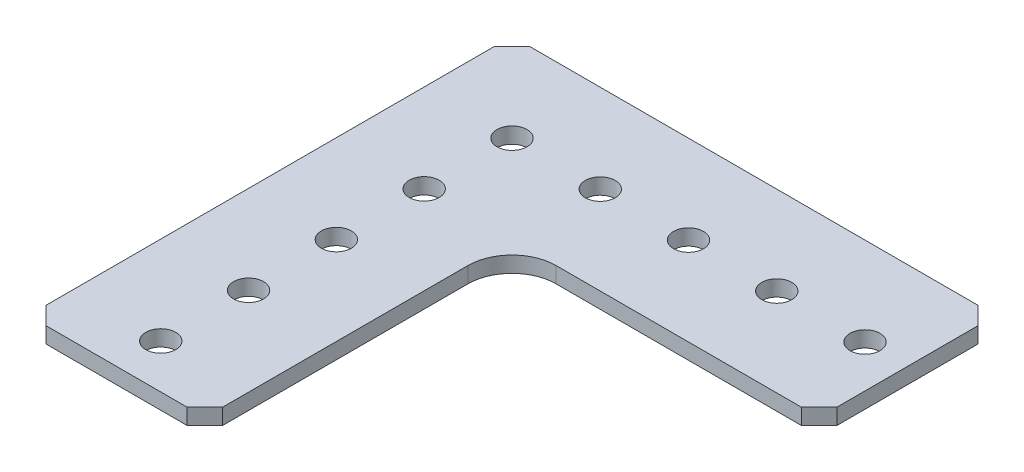
SolidWorks part; units mm, degrees
ref_plane "Front Plane" through (0, 0, 0) normal (0, 0, 1) x (1, 0, 0)
ref_plane "Top Plane" through (0, 0, 0) normal (0, 1, 0) x (1, 0, 0)
ref_plane "Right Plane" through (0, 0, 0) normal (1, 0, 0) x (0, 0, -1)
sketch "Sketch2" plane through (0, 0, 0) normal (0, 1, 0) x (1, 0, 0)
  line L0 (-39.4869, -27.3737) -> (-39.4869, 37.1423)
  line L1 (-36.9469, 39.6823) -> (27.5691, 39.6823)
  line L2 (30.1091, 37.1423) -> (30.1091, 16.8223)
  line L3 (27.5691, 14.2823) -> (-7.7369, 14.2823)
  line L4 (-14.0869, 7.9323) -> (-14.0869, -27.3737)
  line L5 (-16.6269, -29.9137) -> (-36.9469, -29.9137)
  line L6 (-39.4869, 37.1423) -> (-36.9469, 39.6823)
  line L7 (-36.9469, -29.9137) -> (-39.4869, -27.3737)
  line L8 (-14.0869, -27.3737) -> (-16.6269, -29.9137)
  line L9 (27.5691, 39.6823) -> (30.1091, 37.1423)
  line L10 (30.1091, 16.8223) -> (27.5691, 14.2823)
  arc A0 (-7.7369, 14.2823) -> (-14.0869, 7.9323) centre (-7.7369, 7.9323) ccw
  circle A1 centre (-26.7869, 26.9823) radius 2.159
  circle A2 centre (-14.0869, 26.9823) radius 2.159
  circle A3 centre (-1.3869, 26.9823) radius 2.159
  circle A4 centre (11.3131, 26.9823) radius 2.159
  circle A5 centre (24.0131, 26.9823) radius 2.159
  circle A6 centre (-26.7869, 14.3458) radius 2.159
  circle A7 centre (-26.7869, 1.7093) radius 2.159
  circle A8 centre (-26.7869, -10.9272) radius 2.159
  circle A9 centre (-26.7869, -23.5637) radius 2.159
  point P0 (-39.4869, -29.9137)
  point P1 (-39.4869, 39.6823)
  point P3 (30.1091, 39.6823)
  point P4 (30.1091, 14.2823)
  point P5 (-14.0869, -29.9137)
  dimension "D5" = 6.35
  dimension "D6" = 12.7
  dimension "D8" = 5
  dimension "D1" = 69.596
  dimension "D2" = 69.596
  dimension "D3" = 20.32
  dimension "D4" = 20.32
  dimension "D7" = 12.7
  dimension "D9" = 6.096
  dimension "D11" = 6.35
  dimension "D10" = 5
extrude "Boss-Extrude2" add sketch "Sketch2" along normal blind 2.286
